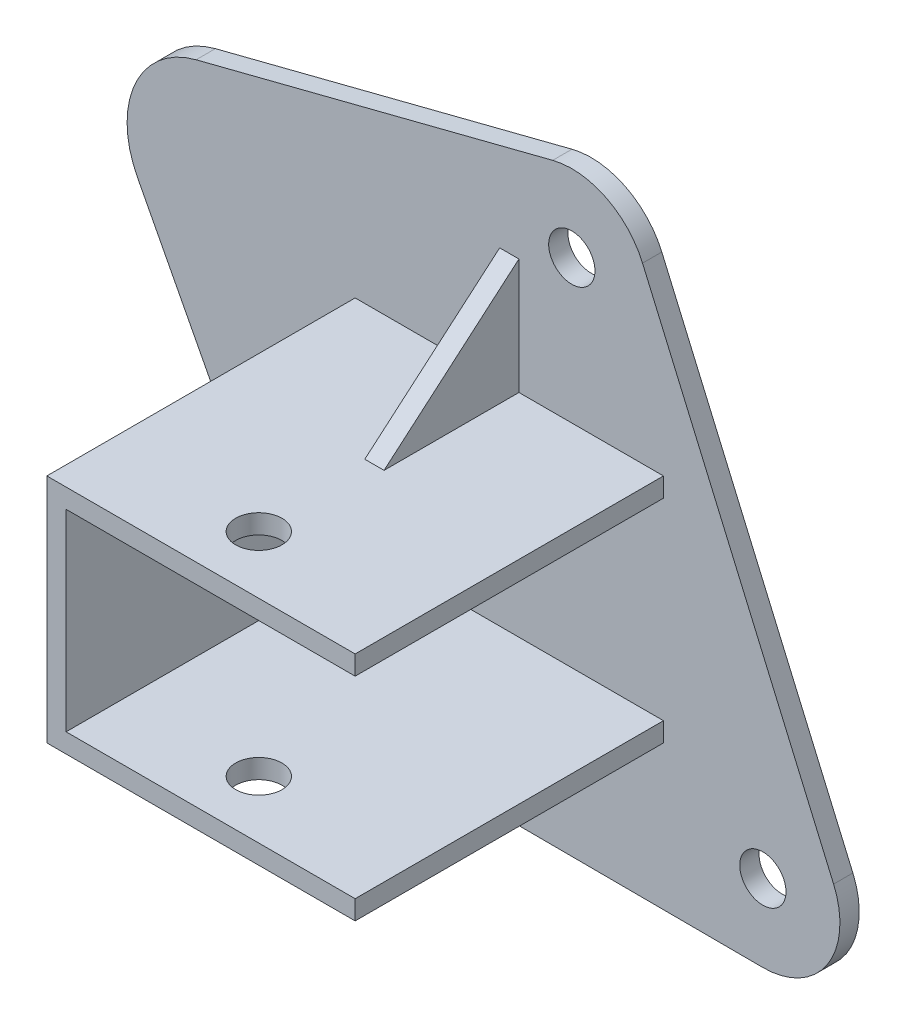
SolidWorks part; units mm, degrees
ref_plane "Plan de face" through (0, 0, 0) normal (0, 0, 1) x (1, 0, 0)
ref_plane "Plan de dessus" through (0, 0, 0) normal (0, 1, 0) x (1, 0, 0)
ref_plane "Plan de droite" through (0, 0, 0) normal (1, 0, 0) x (0, 0, -1)
sketch "Esquisse1" plane through (0, 0, 0) normal (0, 0, 1) x (1, 0, 0)
  line L0 (0, 0) -> (0, 233.9621) construction
  line L1 (0, 0) -> (-773.4584, 0) construction
  line L3 (-680.4142, -25.5607) -> (-407.8894, -25.5607)
  line L4 (-680.4142, -25.5607) -> (-680.4142, 147.8474)
  line L5 (-680.4142, 147.8474) -> (-407.8894, 147.8474)
  line L6 (-407.8894, -25.5607) -> (-407.8894, 147.8474)
  circle A0 centre (-580.4208, 0.3676) radius 6
  circle A1 centre (-480.4215, 0) radius 6
  circle A2 centre (-530, 114.7474) radius 6
  point P5 (-577.5, -2.1719)
  point P9 (-535.2549, 110.8126)
  point P14 (-580.4208, 0)
  dimension "D4" = 100
  dimension "D5" = 12
  dimension "D6" = 12
  dimension "D7" = 125
  dimension "D8" = 12
  dimension "D17" = 530
  dimension "D19" = 125
  dimension "D20" = 480.4215
  dimension "D21" = 480.4215
extrude "Boss.-Extru.1" add sketch "Esquisse1" along normal blind 5
sketch "Esquisse2" plane through (0, 0, 5) normal (0, 0, 1) x (1, 0, 0)
  line L0 (-534.956, 134.1237) -> (-627.4813, 110.4577)
  line L1 (-642.6803, 76.3829) -> (-598.1491, -8.8904)
  line L2 (-580.4944, -19.6322) -> (-480.495, -19.9999)
  line L3 (-511.6404, 122.68) -> (-462.0619, 7.9326)
  arc A0 (-627.4813, 110.4577) -> (-642.6803, 76.3829) centre (-621.5837, 87.4) ccw
  arc A1 (-511.6404, 122.68) -> (-534.956, 134.1237) centre (-530, 114.7474) ccw
  arc A2 (-480.495, -19.9999) -> (-462.0619, 7.9326) centre (-480.4215, 0) ccw
  arc A3 (-598.1491, -8.8904) -> (-580.4944, -19.6322) centre (-580.4208, 0.3676) ccw
  circle A4 centre (-530, 114.7474) radius 6 construction
  point P7 (0, 0)
  point P17 (-521.1879, 132.7015)
  dimension "D1" = 20
  dimension "D2" = 40
  dimension "D4" = 20
extrude "Enlèv. mat.-Extru.1" cut sketch "Esquisse2" against normal up to next (5 mm away) flip side to cut
sketch "Esquisse3" plane through (0, 0, 5) normal (0, 0, 1) x (1, 0, 0)
  line L1 (-586.2131, 77.5748) -> (-506.2131, 77.5748)
  line L2 (-586.2131, 77.5748) -> (-586.2131, 72.5748)
  line L3 (-581.2131, 72.5748) -> (-506.2131, 72.5748)
  line L4 (-506.2131, 77.5748) -> (-506.2131, 72.5748)
  line L5 (-506.2131, 17.5748) -> (-586.2131, 17.5748)
  line L6 (-506.2131, 17.5748) -> (-506.2131, 22.5748)
  line L7 (-506.2131, 22.5748) -> (-581.2131, 22.5748)
  line L8 (-586.2131, 17.5748) -> (-586.2131, 22.5748)
  line L10 (-586.2131, 22.5748) -> (-586.2131, 72.5748)
  line L12 (-581.2131, 22.5748) -> (-581.2131, 72.5748)
  dimension "D1" = 5
  dimension "D2" = 5
  dimension "D3" = 50
  dimension "D4" = 80
  dimension "D5" = 80
  dimension "D6" = 5
extrude "Boss.-Extru.2" add sketch "Esquisse3" along normal blind 80
sketch "Esquisse4" plane through (0, 77.5748, 0) normal (0, 1, 0) x (1, 0, 0)
  line L0 (-506.2131, -85) -> (-586.2131, -85) construction
  line L1 (-506.2131, -85) -> (-506.2131, -5) construction
  circle A0 centre (-546.2131, -70) radius 6
  dimension "D1" = 12
  dimension "D2" = 15
  dimension "D3" = 40
extrude "Enlèv. mat.-Extru.2" cut sketch "Esquisse4" against normal through all
ref_plane "Plan1" through (-546.2131, 0, 0) normal (-1, 0, 0) x (0, 0, 1)
sketch "Esquisse5" plane through (-546.2131, 0, 0) normal (-1, 0, 0) x (0, 0, 1)
  line L0 (5, 107.5748) -> (40, 77.5748)
  line L1 (5, 7.9326) -> (5, 122.68) construction
  line L2 (85, 77.5748) -> (5, 77.5748) construction
  line L3 (40, 77.5748) -> (5, 77.5748)
  line L4 (5, 77.5748) -> (5, 107.5748)
  line L5 (5, 17.5748) -> (5, -12.4252)
  line L6 (5, -20) -> (5, 7.9326) construction
  line L7 (5, -12.4252) -> (40, 17.5748)
  line L8 (85, 17.5748) -> (5, 17.5748) construction
  line L9 (40, 17.5748) -> (5, 17.5748)
  dimension "D1" = 30
  dimension "D2" = 35
  dimension "D3" = 35
  dimension "D4" = 30
extrude "Boss.-Extru.3" add sketch "Esquisse5" along normal mid plane 5
